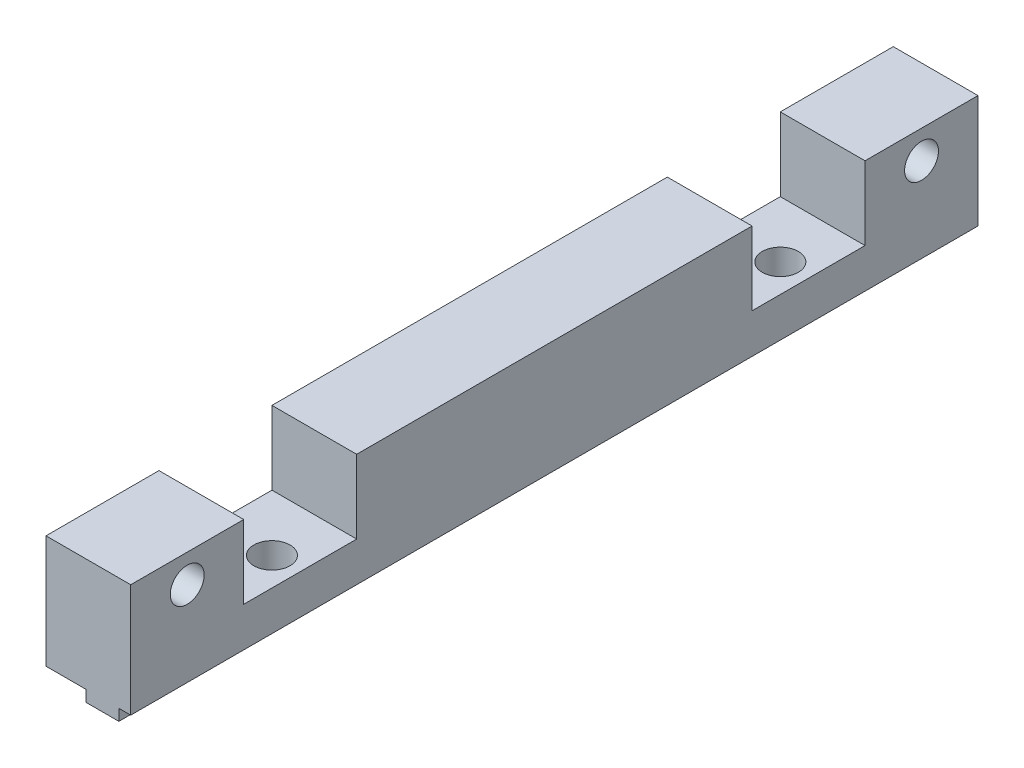
SolidWorks part; units mm, degrees
ref_plane "Front Plane" through (0, 0, 0) normal (0, 0, 1) x (1, 0, 0)
ref_plane "Top Plane" through (0, 0, 0) normal (0, 1, 0) x (1, 0, 0)
ref_plane "Right Plane" through (0, 0, 0) normal (1, 0, 0) x (0, 0, -1)
sketch "Esquisse1" plane through (0, 0, 0) normal (0, 0, 1) x (1, 0, 0)
  line L0 (0, 10) -> (7.5, 10)
  line L1 (7.5, 10) -> (7.5, 0)
  line L2 (7.5, 0) -> (6.45, 0)
  line L3 (6.45, 0) -> (6.45, -1)
  line L4 (6.45, -1) -> (3.55, -1)
  line L5 (3.55, -1) -> (3.55, 0)
  line L6 (3.55, 0) -> (0, 0)
  line L7 (0, 0) -> (0, 10)
  point P3 (1.9986, -1.7286)
  point P9 (0, 0)
  point P11 (10, 0)
  dimension "D1" = 7.5
  dimension "D2" = 10
  dimension "D3" = 1
  dimension "D4" = 2.9
  dimension "D5" = 3.55
extrude "Main" add sketch "Esquisse1" along normal blind 75
sketch "Esquisse2" plane through (7.5, 0, 0) normal (1, 0, 0) x (0, 0, -1)
  line L0 (0, 0) -> (0, 10) construction
  line L2 (-75, 0) -> (0, 0) construction
  circle A0 centre (-5, 7.5) radius 1.5
  circle A1 centre (-70, 7.5) radius 1.5
  point P8 (-3.283, 0)
  point P9 (0, 0)
  dimension "D1" = 65
  dimension "D4" = 3
  dimension "D2" = 5
  dimension "D3" = 7.5
extrude "Enlèv. mat.-Extru.1" cut sketch "Esquisse2" against normal through all
sketch "Esquisse3" plane through (7.5, 0, 0) normal (1, 0, 0) x (0, 0, -1)
  line L0 (-75, 10) -> (0, 10) construction
  line L1 (-65, 10) -> (-55, 10)
  line L2 (-65, 10) -> (-65, 3.5)
  line L3 (-65, 3.5) -> (-55, 3.5)
  line L4 (-55, 10) -> (-55, 3.5)
  line L5 (-75, 0) -> (-75, 10) construction
  line L9 (0, 0) -> (0, 10) construction
  line L10 (-20, 10) -> (-10, 10)
  line L11 (-20, 10) -> (-20, 3.5)
  line L12 (-20, 3.5) -> (-10, 3.5)
  line L13 (-10, 10) -> (-10, 3.5)
  line L14 (-75, 0) -> (0, 0) construction
  dimension "D1" = 10
  dimension "D2" = 10
  dimension "D3" = 3.5
  dimension "D4" = 10
  dimension "D5" = 10
extrude "Enlèv. mat.-Extru.2" cut sketch "Esquisse3" against normal through all
sketch "Esquisse4" plane through (0, -1, 0) normal (0, -1, 0) x (-1, 0, 0)
  line L0 (0, -75) -> (0, 0) construction
  line L1 (-3.55, -75) -> (-6.45, -75) construction
  line L2 (-3.55, 0) -> (-6.45, 0) construction
  circle A0 centre (-5, -60) radius 1.6
  circle A1 centre (-5, -15) radius 1.6
  point P6 (0, 0)
  dimension "D1" = 3.2
  dimension "D2" = 5
  dimension "D3" = 15
  dimension "D4" = 15
extrude "Enlèv. mat.-Extru.3" cut sketch "Esquisse4" against normal through all
